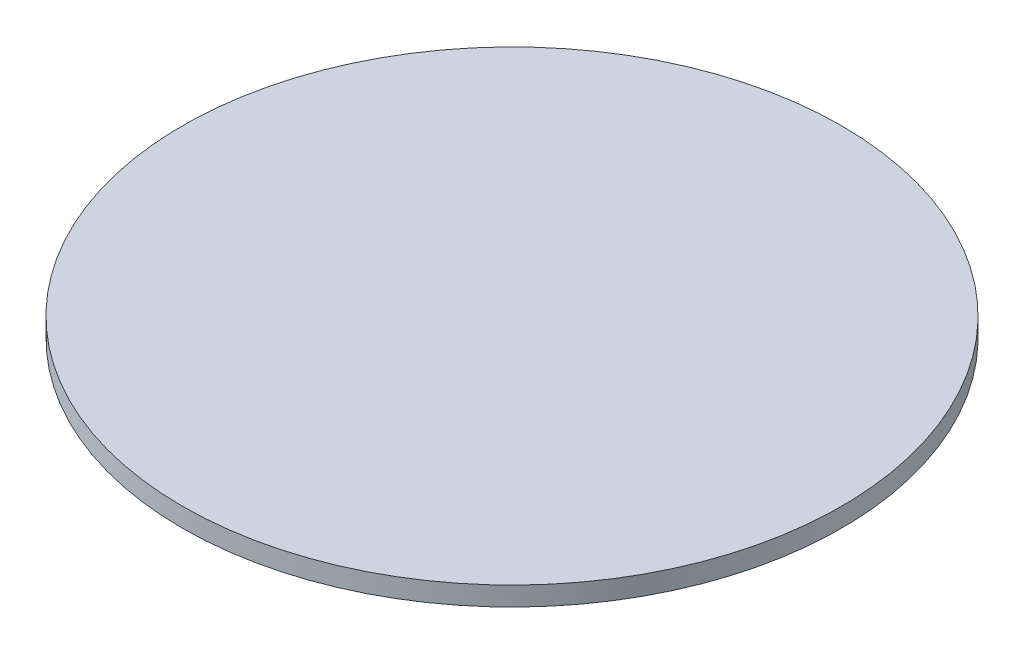
SolidWorks part; units mm, degrees
ref_plane "Front Plane" through (0, 0, 0) normal (0, 0, 1) x (1, 0, 0)
ref_plane "Top Plane" through (0, 0, 0) normal (0, 1, 0) x (1, 0, 0)
ref_plane "Right Plane" through (0, 0, 0) normal (1, 0, 0) x (0, 0, -1)
sketch "Sketch1" plane through (0, 0, 0) normal (0, 1, 0) x (1, 0, 0)
  circle A0 centre (0, 0) radius 17.3
  dimension "D1" = 34.6
extrude "Boss-Extrude1" add sketch "Sketch1" along normal blind 1
